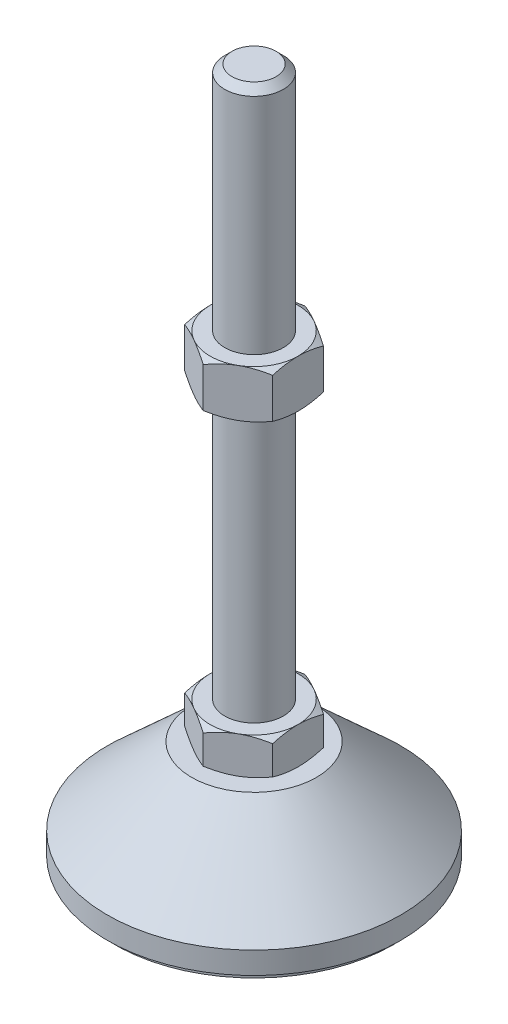
SolidWorks part; units mm, degrees
ref_plane "Спереди" through (0, 0, 0) normal (0, 0, 1) x (1, 0, 0)
ref_plane "Сверху" through (0, 0, 0) normal (0, 1, 0) x (1, 0, 0)
ref_plane "Справа" through (0, 0, 0) normal (1, 0, 0) x (0, 0, -1)
sketch "Эскиз1" plane through (0, 0, 0) normal (0, 0, 1) x (1, 0, 0)
  line L0 (0, 0) -> (-38, 0)
  line L1 (-38, 0) -> (-38, 2)
  line L2 (-38, 2) -> (-40, 2)
  line L3 (-40, 2) -> (-40, 8)
  line L4 (-40, 8) -> (-17, 29)
  line L5 (-17, 29) -> (-8, 29)
  line L12 (-8, 39) -> (-8, 187)
  line L13 (-8, 187) -> (-6, 189)
  line L14 (-6, 189) -> (0, 189)
  line L15 (0, 189) -> (0, 0) construction
  line L16 (-8, 29) -> (0, 29) construction
  line L17 (0, 0) -> (0, 189)
  line L18 (0, 0) -> (0, -7.9595) construction
  line L19 (-8, 39) -> (-8, 29)
  point P8 (-8, 113)
  point P23 (-12.5, 29)
  dimension "D1" = 16
  dimension "D2" = 29
  dimension "D3" = 10
  dimension "D4" = 80
  dimension "D5" = 8
  dimension "D6" = 2
  dimension "D7" = 45
  dimension "D8" = 34
  dimension "D9" = 2
  dimension "D10" = 150
  dimension "D11" = 6
revolve "Повернуть1" add sketch "Эскиз1" angle 360 about L17
sketch "Эскиз2" plane through (0, 29, 0) normal (0, 1, 0) x (1, 0, 0)
  line L1 (0, 13.8564) -> (-12, 6.9282)
  line L2 (-12, 6.9282) -> (-12, -6.9282)
  line L3 (-12, -6.9282) -> (0, -13.8564)
  line L4 (0, -13.8564) -> (12, -6.9282)
  line L5 (12, -6.9282) -> (12, 6.9282)
  line L6 (12, 6.9282) -> (0, 13.8564)
  circle A0 centre (0, 0) radius 12 construction
  dimension "D1" = 24
extrude "Бобышка-Вытянуть1" add sketch "Эскиз2" along normal up to vertex (10 mm away) up to point (-8, 39, 0)
ref_plane "Плоскость1" through (0, 113, 0) normal (0, 1, 0) x (1, 0, 0)
sketch "Эскиз3" plane through (0, 113, 0) normal (0, 1, 0) x (1, 0, 0)
  line L6 (12, 6.9282) -> (0, 13.8564)
  line L7 (0, 13.8564) -> (-12, 6.9282)
  line L8 (-12, 6.9282) -> (-12, -6.9282)
  line L9 (-12, -6.9282) -> (0, -13.8564)
  line L10 (0, -13.8564) -> (12, -6.9282)
  line L11 (12, -6.9282) -> (12, 6.9282)
  line L12 (12, 6.9282) -> (0, 13.8564)
  line L13 (0, 13.8564) -> (-12, 6.9282)
  line L14 (-12, 6.9282) -> (-12, -6.9282)
  line L15 (-12, -6.9282) -> (0, -13.8564)
  line L16 (0, -13.8564) -> (12, -6.9282)
  line L17 (12, -6.9282) -> (12, 6.9282)
  dimension "D1" = 0
extrude "Бобышка-Вытянуть2" add sketch "Эскиз3" along normal blind 13
sketch "Эскиз4" plane through (0, 0, 0) normal (0, 0, 1) x (1, 0, 0)
  line L0 (-12, 126) -> (-23.2583, 119.5)
  line L1 (-23.2583, 119.5) -> (-23.2583, 126)
  line L2 (-23.2583, 126) -> (-12, 126)
  line L3 (-23.2583, 119.5) -> (-12, 113)
  line L4 (50, 113) -> (-50, 113) construction
  line L5 (-12, 113) -> (-23.2583, 113)
  line L6 (-23.2583, 113) -> (-23.2583, 119.5)
  line L7 (-12, 126) -> (-12, 113) construction
  line L8 (-12, 39) -> (-20.6603, 39)
  line L9 (-20.6603, 39) -> (-20.6603, 34)
  line L10 (-20.6603, 34) -> (-12, 39)
  line L11 (-12, 29) -> (-20.6603, 34)
  line L12 (-20.6603, 34) -> (-20.6603, 29)
  line L13 (-20.6603, 29) -> (-12, 29)
  line L14 (0, 189) -> (0, 96.3793) construction
  dimension "D1" = 30
  dimension "D2" = 30
revolve "Вырез-Повернуть2" cut sketch "Эскиз4" angle 360 about L14
